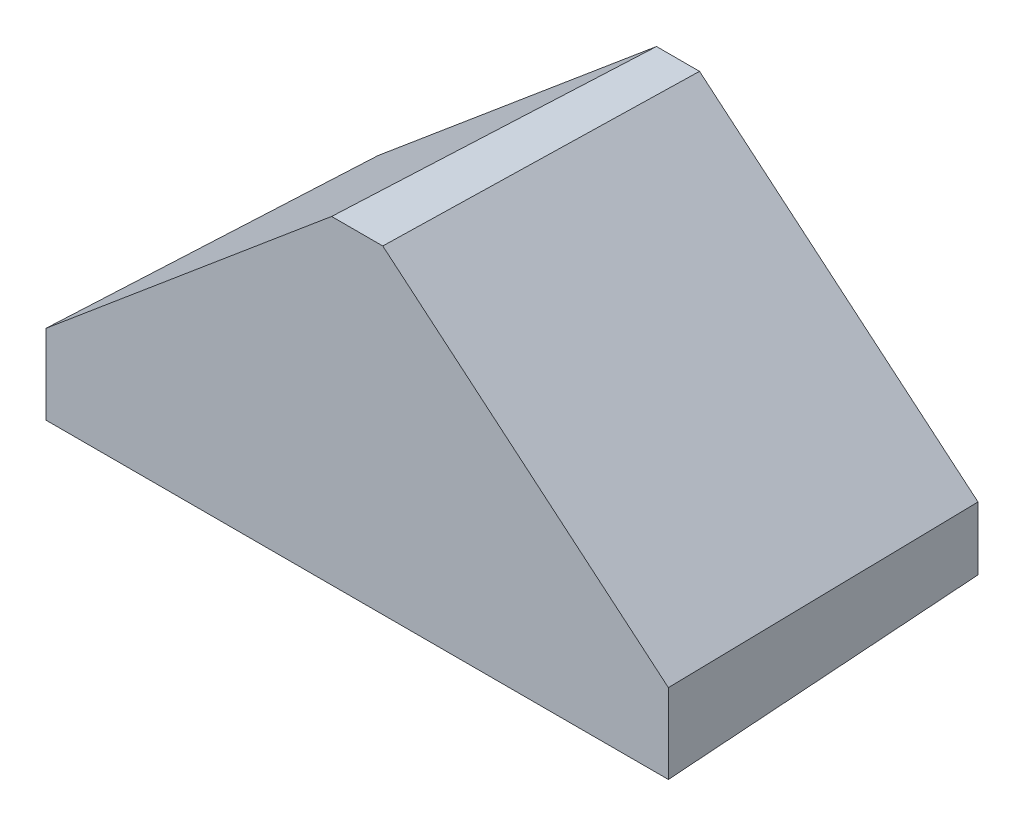
SolidWorks part; units mm, degrees
ref_plane "Alzado" through (0, 0, 0) normal (0, 0, 1) x (1, 0, 0)
ref_plane "Planta" through (0, 0, 0) normal (0, 1, 0) x (1, 0, 0)
ref_plane "Vista lateral" through (0, 0, 0) normal (1, 0, 0) x (0, 0, -1)
sketch "Croquis6" plane through (0, 0, 0) normal (0, 0, 1) x (1, 0, 0)
  line L1 (0, 0) -> (0, 10)
  line L2 (0, 10) -> (44.0949, 47)
  line L3 (44.0949, 47) -> (50.9051, 47)
  line L4 (50.9051, 47) -> (95, 10)
  line L5 (95, 10) -> (95, 0)
  line L7 (0, 10) -> (0.1282, 10) construction
  line L8 (95, 10) -> (119.0311, 10) construction
  line L9 (0, 0) -> (95, 0)
  dimension "D1" = 95
  dimension "D2" = 10
  dimension "D3" = 40
  dimension "D4" = 40
  dimension "D5" = 47
extrude "Saliente-Extruir3" add sketch "Croquis6" along normal blind 50.8 draft 2 draft outward yes
sketch "Croquis7" plane through (0, 0, 50.8) normal (0, 0, 1) x (1, 0, 0)
  line L6 (-1.774, -1.774) -> (96.774, -1.774)
  line L7 (96.774, -1.774) -> (96.774, 10.8272)
  line L8 (96.774, 10.8272) -> (51.5508, 48.774)
  line L9 (51.5508, 48.774) -> (43.4492, 48.774)
  line L10 (43.4492, 48.774) -> (-1.774, 10.8272)
  line L11 (-1.774, 10.8272) -> (-1.774, -1.774)
  line L12 (-1.774, -1.774) -> (96.774, -1.774)
  line L13 (96.774, -1.774) -> (96.774, 10.8272)
  line L14 (96.774, 10.8272) -> (51.5508, 48.774)
  line L15 (51.5508, 48.774) -> (43.4492, 48.774)
  line L16 (43.4492, 48.774) -> (-1.774, 10.8272)
  line L17 (-1.774, 10.8272) -> (-1.774, -1.774)
  dimension "D2" = 98.548
  dimension "D3" = 12.6012
  dimension "D4" = 59.0347
  dimension "D5" = 8.1016
  dimension "D6" = 59.0347
  dimension "D7" = 12.6012
  dimension "D1" = 0
sketch "Croquis8" plane through (0, 0, 50.8) normal (0, 0, 1) x (1, 0, 0)
  line L6 (-1.774, -1.774) -> (96.774, -1.774)
  line L7 (96.774, -1.774) -> (96.774, 10.8272)
  line L8 (96.774, 10.8272) -> (51.5508, 48.774)
  line L9 (51.5508, 48.774) -> (43.4492, 48.774)
  line L10 (43.4492, 48.774) -> (-1.774, 10.8272)
  line L11 (-1.774, 10.8272) -> (-1.774, -1.774)
  line L12 (-1.774, -1.774) -> (96.774, -1.774)
  line L13 (96.774, -1.774) -> (96.774, 10.8272)
  line L14 (96.774, 10.8272) -> (51.5508, 48.774)
  line L15 (51.5508, 48.774) -> (43.4492, 48.774)
  line L16 (43.4492, 48.774) -> (-1.774, 10.8272)
  line L17 (-1.774, 10.8272) -> (-1.774, -1.774)
  dimension "D2" = 98.548
  dimension "D3" = 12.6012
  dimension "D4" = 59.0347
  dimension "D5" = 8.1016
  dimension "D6" = 59.0347
  dimension "D7" = 12.6012
  dimension "D1" = 0
